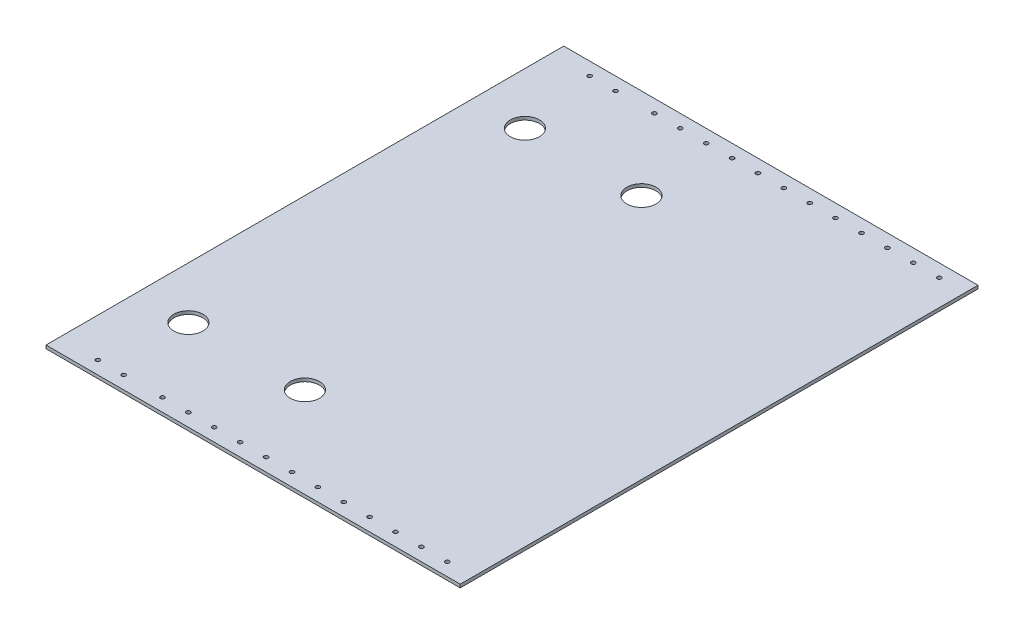
SolidWorks part; units mm, degrees
material "Lexan"
ref_plane "Front Plane" through (0, 0, 0) normal (0, 0, 1) x (1, 0, 0)
ref_plane "Top Plane" through (0, 0, 0) normal (0, 1, 0) x (1, 0, 0)
ref_plane "Right Plane" through (0, 0, 0) normal (1, 0, 0) x (0, 0, -1)
sketch "Sketch1" plane through (0, 0, 0) normal (0, 1, 0) x (1, 0, 0)
  line L1 (0, 0) -> (571.5, 0)
  line L2 (0, 0) -> (0, 508)
  line L3 (0, 508) -> (571.5, 508)
  line L4 (571.5, 0) -> (571.5, 508)
  dimension "D1" = 571.5
  dimension "D2" = 508
extrude "Boss-Extrude1" add sketch "Sketch1" along normal blind 3.175
sketch "Sketch2" plane through (0, 3.175, 0) normal (0, 1, 0) x (1, 0, 0)
  line L0 (273.05, 419.1) -> (273.05, 508) construction
  line L1 (215.9, 419.1) -> (330.2, 419.1) construction
  line L3 (215.9, 88.9) -> (330.2, 88.9) construction
  line L4 (571.5, 0) -> (571.5, 508) construction
  line L5 (571.5, 508) -> (0, 508) construction
  line L6 (273.05, 88.9) -> (273.05, 0) construction
  line L7 (0, 0) -> (571.5, 0) construction
  circle A0 centre (215.9, 419.1) radius 14.2875
  circle A1 centre (330.2, 419.1) radius 14.2875
  circle A2 centre (215.9, 88.9) radius 14.2875
  circle A3 centre (330.2, 88.9) radius 14.2875
  dimension "D1" = 28.575
  dimension "D2" = 28.575
  dimension "D3" = 28.575
  dimension "D4" = 28.575
  dimension "D5" = 114.3
  dimension "D6" = 114.3
  dimension "D7" = 330.2
  dimension "D8" = 241.3
extrude "Cut-Extrude1" cut sketch "Sketch2" against normal blind 3.175
sketch "Sketch4" plane through (0, 3.175, 0) normal (0, 1, 0) x (1, 0, 0)
  line L0 (571.5, 495.3) -> (0, 495.3) construction
  line L1 (571.5, 0) -> (571.5, 508) construction
  line L2 (0, 508) -> (0, 0) construction
  line L3 (571.5, 508) -> (0, 508) construction
  line L4 (0, 254) -> (571.5, 254) construction
  line L5 (571.5, 12.7) -> (0, 12.7) construction
  circle A0 centre (546.1, 495.3) radius 2.0193
  circle A1 centre (520.7, 495.3) radius 2.0193
  circle A2 centre (495.3, 495.3) radius 2.0193
  circle A3 centre (469.9, 495.3) radius 2.0193
  circle A4 centre (444.5, 495.3) radius 2.0193
  circle A5 centre (419.1, 495.3) radius 2.0193
  circle A6 centre (393.7, 495.3) radius 2.0193
  circle A7 centre (368.3, 495.3) radius 2.0193
  circle A8 centre (342.9, 495.3) radius 2.0193
  circle A9 centre (317.5, 495.3) radius 2.0193
  circle A10 centre (292.1, 495.3) radius 2.0193
  circle A11 centre (266.7, 495.3) radius 2.0193
  circle A12 centre (228.6, 495.3) radius 2.0193
  circle A13 centre (203.2, 495.3) radius 2.0193
  circle A14 centre (203.2, 12.7) radius 2.0193
  circle A15 centre (228.6, 12.7) radius 2.0193
  circle A16 centre (266.7, 12.7) radius 2.0193
  circle A17 centre (292.1, 12.7) radius 2.0193
  circle A18 centre (317.5, 12.7) radius 2.0193
  circle A19 centre (342.9, 12.7) radius 2.0193
  circle A20 centre (368.3, 12.7) radius 2.0193
  circle A21 centre (393.7, 12.7) radius 2.0193
  circle A22 centre (419.1, 12.7) radius 2.0193
  circle A23 centre (444.5, 12.7) radius 2.0193
  circle A24 centre (469.9, 12.7) radius 2.0193
  circle A25 centre (495.3, 12.7) radius 2.0193
  circle A26 centre (520.7, 12.7) radius 2.0193
  circle A27 centre (546.1, 12.7) radius 2.0193
  dimension "D2" = 4.0386
  dimension "D3" = 25.4
  dimension "D5" = 38.1
  dimension "D6" = 25.4
  dimension "D1" = 12.7
  dimension "D4" = 12
extrude "Cut-Extrude3" cut sketch "Sketch4" against normal through all both
sketch "Sketch5" plane through (0, 0, 0) normal (-1, 0, 0) x (0, 0, 1)
  line L1 (-567.431, 71.2281) -> (52.1486, 71.2281)
  line L2 (-567.431, 71.2281) -> (-567.431, -17.807)
  line L3 (-567.431, -17.807) -> (52.1486, -17.807)
  line L4 (52.1486, 71.2281) -> (52.1486, -17.807)
extrude "Cut-Extrude4" cut sketch "Sketch5" against normal blind 165.1
